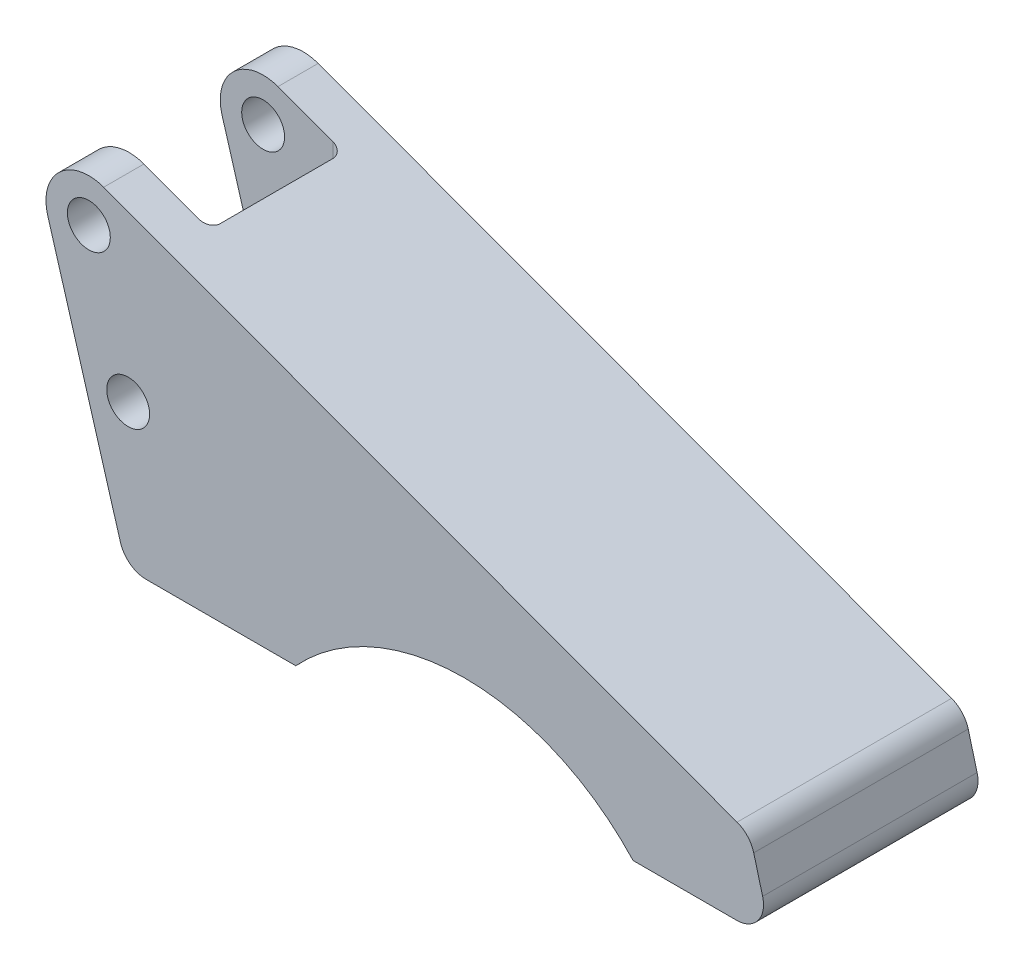
SolidWorks part; units mm, degrees
ref_plane "Front Plane" through (0, 0, 0) normal (0, 0, 1) x (1, 0, 0)
ref_plane "Top Plane" through (0, 0, 0) normal (0, 1, 0) x (1, 0, 0)
ref_plane "Right Plane" through (0, 0, 0) normal (1, 0, 0) x (0, 0, -1)
sketch "Sketch1" plane through (0, 0, 0) normal (0, 0, 1) x (1, 0, 0)
  line L0 (6.9475, -51.87) -> (-7.6736, -2.2617)
  line L1 (38.5852, -51.87) -> (6.9475, -51.87)
  line L2 (101.4948, -51.87) -> (127.33, -51.87)
  line L3 (127.33, -51.87) -> (123.33, -36.87)
  line L4 (123.33, -36.87) -> (2.7634, 7.5076)
  circle A0 centre (0, 0) radius 4
  circle A1 centre (7.33, -24.87) radius 4
  arc A2 (2.7634, 7.5076) -> (-7.6736, -2.2617) centre (0, 0) ccw
  arc A4 (101.4948, -51.87) -> (38.5852, -51.87) centre (70.04, -80.88) ccw
  dimension "D1" = 8
  dimension "D2" = 8
  dimension "D5" = 16
  dimension "D6" = 6.9475
  dimension "D9" = 85.58
  dimension "D3" = 7.33
  dimension "D4" = 24.87
  dimension "D7" = 62.71
  dimension "D8" = 56.01
  dimension "D10" = 120
  dimension "D11" = 116
  dimension "D12" = 27
  dimension "D13" = 12
extrude "Boss-Extrude1" add sketch "Sketch1" against normal blind 40
fillet "Fillet1" radius 5 3 edges at (127.33, -51.87, -20) (123.33, -36.87, -20) (6.9475, -51.87, -20)
sketch "Sketch2" plane through (0, 0, 0) normal (0, 1, 0) x (1, 0, 0)
  line L0 (120.8946, 0) -> (2.7634, 0) construction
  line L1 (-10, 32.5) -> (15, 32.5)
  line L2 (-10, 32.5) -> (-10, 7.5)
  line L3 (-10, 7.5) -> (15, 7.5)
  line L4 (15, 32.5) -> (15, 7.5)
  dimension "D1" = 25
  dimension "D2" = 7.5
  dimension "D3" = 25
  dimension "D4" = 15
extrude "Cut-Extrude1" cut sketch "Sketch2" against normal through all both and the other way through all
fillet "Fillet2" radius 2 2 edges at (15, -24.4332, -7.5) (15, -24.4332, -32.5)
